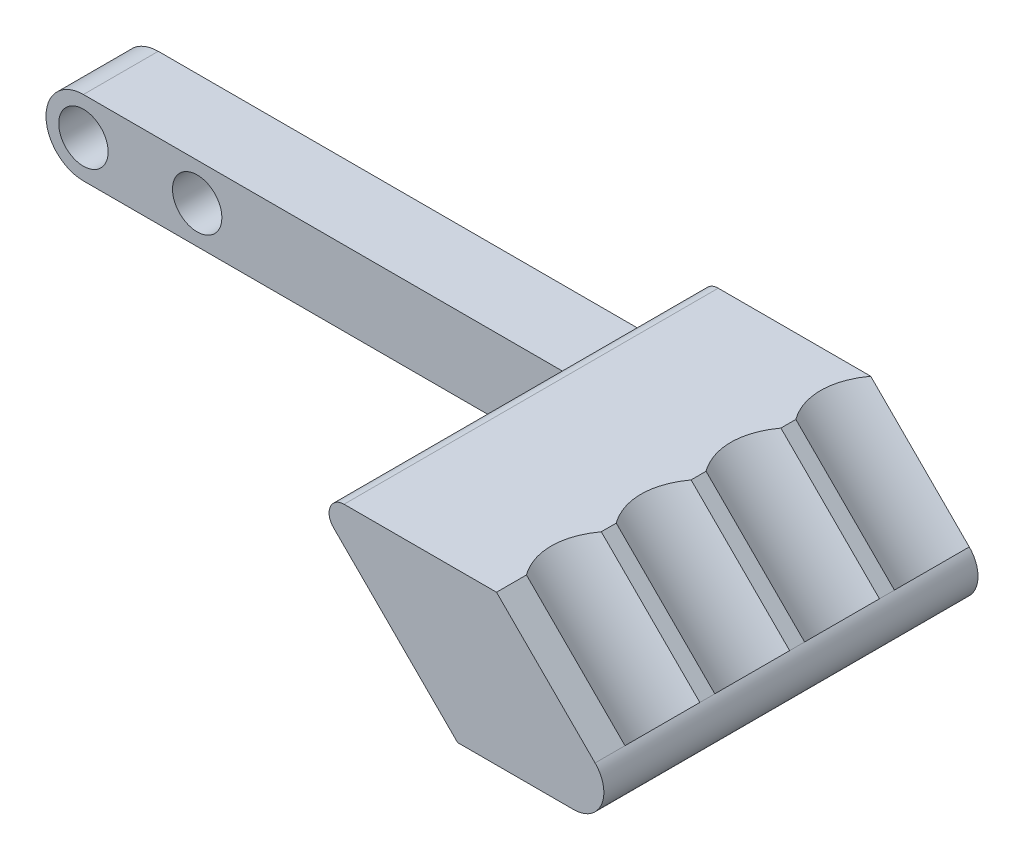
SolidWorks part; units mm, degrees
ref_plane "前视基准面" through (0, 0, 0) normal (0, 0, 1) x (1, 0, 0)
ref_plane "上视基准面" through (0, 0, 0) normal (0, 1, 0) x (1, 0, 0)
ref_plane "右视基准面" through (0, 0, 0) normal (1, 0, 0) x (0, 0, -1)
other "Configuration Table"
sketch "Sketch2" plane through (0, 0, 0) normal (0, 0, 1) x (1, 0, 0)
  line L0 (0, 2.5) -> (40, 2.5)
  line L1 (0, -2.5) -> (57.6, -2.5)
  line L2 (40, 2.5) -> (35, 7.5)
  line L3 (57.6, -2.5) -> (61.3114, 1.2114)
  line L4 (57.6, -2.5) -> (47.6, 7.5)
  line L5 (35, 7.5) -> (47.6, 7.5)
  circle A0 centre (0, 0) radius 1.65
  circle A1 centre (0, 0) radius 2.5
  circle A2 centre (7.6, 0) radius 1.65
  point P12 (0, 0)
  dimension "D1" = 3.3
  dimension "D2" = 5
  dimension "D8" = 3.3
  dimension "D9" = 7.6
  dimension "D3" = 45
  dimension "D4" = 135
  dimension "D5" = 57.6
  dimension "D6" = 40
  dimension "D7" = 5
extrude "Boss-Extrude1" add sketch "Sketch2" along normal blind 5 contours A1 A0 | A1 L1 L4 L5 L2 L0
fillet "Fillet1" radius 2 1 edges at (57.6, -2.5, 2.5)
fillet "Fillet2" radius 1 1 edges at (40, 2.5, 2.5)
fillet "Fillet3" radius 1 1 edges at (35, 7.5, 2.5)
ref_plane "Plane1" through (26.6358, -26.6358, 0) normal (0.7071, -0.7071, 0) x (0, 0, -1)
sketch "Sketch3" plane through (26.6358, -26.6358, 0) normal (0.7071, -0.7071, 0) x (0, 0, -1)
  line L0 (-5, 38.9616) -> (0, 38.9616) construction
  circle A0 centre (-2.5, 43.8606) radius 5.5
  point P3 (0, 0)
  point P6 (-2.5, 38.9616)
  point P7 (0, 0)
  dimension "D1" = 11
extrude "Cut-Extrude1" cut sketch "Sketch3" against normal blind 34
sketch "Sketch4" plane through (0, 0, 5) normal (0, 0, 1) x (1, 0, 0)
  line L0 (37.4142, 7.5) -> (47.6, 7.5) construction
  line L1 (54.1858, 0.9142) -> (47.6, 7.5) construction
  line L2 (38.2929, 4.2071) -> (36.7071, 5.7929) construction
  line L3 (37.4142, 7.5) -> (47.6, 7.5)
  line L4 (54.1858, 0.9142) -> (47.6, 7.5)
  line L5 (38.2929, 4.2071) -> (36.7071, 5.7929)
  line L6 (38.2929, 4.2071) -> (45, -2.5)
  line L7 (52.7716, -2.5) -> (45, -2.5)
  arc A0 (52.7716, -2.5) -> (54.1858, 0.9142) centre (52.7716, -0.5) ccw construction
  arc A1 (37.4142, 7.5) -> (36.7071, 5.7929) centre (37.4142, 6.5) ccw construction
  arc A2 (52.7716, -2.5) -> (54.1858, 0.9142) centre (52.7716, -0.5) ccw
  arc A3 (37.4142, 7.5) -> (36.7071, 5.7929) centre (37.4142, 6.5) ccw
extrude "Boss-Extrude2" add sketch "Sketch4" along normal blind 20
pattern_linear "LPattern1" count 4 spacing 6 along (0, 0, 1) of "Cut-Extrude1"
